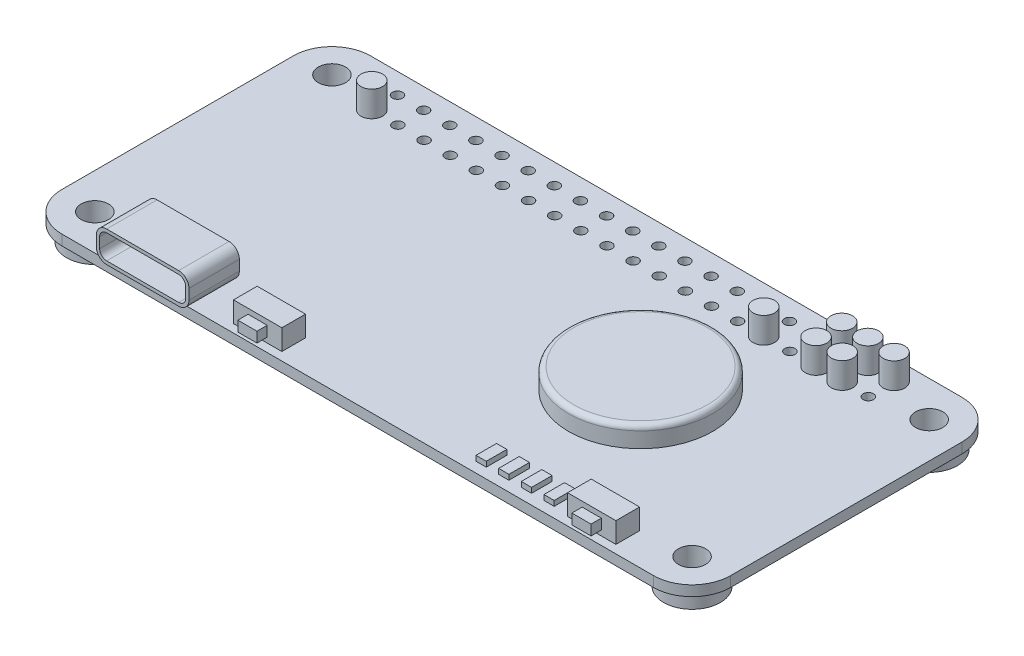
SolidWorks part; units mm, degrees
ref_plane "Front Plane" through (0, 0, 0) normal (0, 0, 1) x (1, 0, 0)
ref_plane "Top Plane" through (0, 0, 0) normal (0, 1, 0) x (1, 0, 0)
ref_plane "Right Plane" through (0, 0, 0) normal (1, 0, 0) x (0, 0, -1)
sketch "Sketch1" plane through (0, 0, 0) normal (0, 1, 0) x (1, 0, 0)
  line L1 (-28.75, 15) -> (28.75, 15)
  line L2 (-32.5, 11.25) -> (-32.5, -11.25)
  line L3 (-28.75, -15) -> (28.75, -15)
  line L4 (32.5, 11.25) -> (32.5, -11.25)
  line L5 (-32.5, 15) -> (32.5, -15) construction
  line L6 (-32.5, -15) -> (32.5, 15) construction
  arc A0 (-32.5, -11.25) -> (-28.75, -15) centre (-28.75, -11.25) ccw
  arc A1 (28.75, -15) -> (32.5, -11.25) centre (28.75, -11.25) ccw
  arc A2 (28.75, 15) -> (32.5, 11.25) centre (28.75, 11.25) cw
  arc A3 (-28.75, 15) -> (-32.5, 11.25) centre (-28.75, 11.25) ccw
  point P0 (0, 0)
  dimension "D3" = 3.75
  dimension "D1" = 65
  dimension "D2" = 30
extrude "Boss-Extrude1" add sketch "Sketch1" along normal blind 1 contours L1 A2 L4 A1 L3 A0 L2 A3
sketch "Sketch2" plane through (0, 1, 0) normal (0, 1, 0) x (1, 0, 0)
  line L0 (0, 15) -> (0, -15) construction
  line L1 (-28.75, 15) -> (28.75, 15) construction
  line L2 (-28.75, -15) -> (28.75, -15) construction
  line L3 (-32.5, 0) -> (32.5, 0) construction
  line L4 (-32.5, 11.25) -> (-32.5, -11.25) construction
  line L5 (32.5, 11.25) -> (32.5, -11.25) construction
  circle A0 centre (-29.025, 11.525) radius 1.325
  circle A2 centre (29.025, 11.525) radius 1.325
  circle A3 centre (29.025, -11.525) radius 1.325
  circle A4 centre (-29.025, -11.525) radius 1.325
  dimension "D1" = 2.65
  dimension "D2" = 2.15
  dimension "D3" = 2.15
extrude "Cut-Extrude1" cut sketch "Sketch2" against normal through all
sketch "Sketch3" plane through (0, 1, 0) normal (0, 1, 0) x (1, 0, 0)
  line L0 (-24.128, 13) -> (-24.128, 10.5) construction
  line L3 (-28.75, 15) -> (28.75, 15) construction
  line L5 (-32.5, 11.25) -> (-32.5, -11.25) construction
  circle A0 centre (-24.128, 13) radius 0.5
  circle A1 centre (-24.128, 10.5) radius 0.5
  dimension "D1" = 1
  dimension "D3" = 1.5
  dimension "D4" = 7.872
  dimension "D2" = 2.5
extrude "Cut-Extrude2" cut sketch "Sketch3" against normal through all
pattern_linear "LPattern1" count 20 spacing 2.54 along (1, 0, 0) of "Cut-Extrude2"
sketch "Sketch15" plane through (0, 0, 15) normal (0, 0, 1) x (1, 0, 0)
  line L0 (-28.75, 1) -> (28.75, 1) construction
  line L2 (-24, 4) -> (-17, 4)
  line L3 (-25, 3) -> (-25, 2)
  line L4 (-24, 1) -> (-17, 1)
  line L5 (-16, 3) -> (-16, 2)
  line L6 (-32.5, 1) -> (-32.5, 0) construction
  line L9 (15.325, 0) -> (15.325, 5.5788) construction
  line L10 (-28.75, 0) -> (28.75, 0) construction
  arc A0 (-17, 4) -> (-16, 3) centre (-17, 3) cw
  arc A1 (-17, 1) -> (-16, 2) centre (-17, 2) ccw
  arc A2 (-25, 2) -> (-24, 1) centre (-24, 2) ccw
  arc A3 (-24, 4) -> (-25, 3) centre (-24, 3) ccw
  point P10 (-16, 4)
  point P13 (-16, 1)
  point P18 (-25, 4)
  dimension "D4" = 1
  dimension "D1" = 9
  dimension "D2" = 3
  dimension "D3" = 7.5
extrude "Boss-Extrude6" add sketch "Sketch15" along normal blind 0.4 and the other way blind 4.5
sketch "Sketch16" plane through (0, 0, 15.4) normal (0, 0, 1) x (1, 0, 0)
  line L4 (-17, 3.68) -> (-24, 3.68)
  line L5 (-17, 3.68) -> (-24, 3.68)
  line L6 (-24.68, 3) -> (-24.68, 2)
  line L7 (-24.68, 3) -> (-24.68, 2)
  line L8 (-24, 1.32) -> (-17, 1.32)
  line L9 (-24, 1.32) -> (-17, 1.32)
  line L10 (-16.32, 2) -> (-16.32, 3)
  line L11 (-16.32, 2) -> (-16.32, 3)
  arc A4 (-16.32, 3) -> (-17, 3.68) centre (-17, 3) ccw
  arc A5 (-16.32, 3) -> (-17, 3.68) centre (-17, 3) ccw
  arc A6 (-24, 3.68) -> (-24.68, 3) centre (-24, 3) ccw
  arc A7 (-24, 3.68) -> (-24.68, 3) centre (-24, 3) ccw
  arc A8 (-24.68, 2) -> (-24, 1.32) centre (-24, 2) ccw
  arc A9 (-24.68, 2) -> (-24, 1.32) centre (-24, 2) ccw
  arc A10 (-17, 1.32) -> (-16.32, 2) centre (-17, 2) ccw
  arc A11 (-17, 1.32) -> (-16.32, 2) centre (-17, 2) ccw
  dimension "D2" = 0.32
extrude "Cut-Extrude9" cut sketch "Sketch16" against normal blind 5.25
sketch "草图1" plane through (0, 1, 0) normal (0, 1, 0) x (1, 0, 0)
  line L1 (-12.87, -11.9) -> (-8.17, -11.9)
  line L2 (-12.87, -11.9) -> (-12.87, -14.2)
  line L3 (-12.87, -14.2) -> (-8.17, -14.2)
  line L4 (-8.17, -11.9) -> (-8.17, -14.2)
  line L5 (-28.75, -15) -> (-24, -15) construction
  line L6 (-16, -10.5) -> (-16, -15.4) construction
  line L7 (32.5, 11.25) -> (32.5, -11.25) construction
  line L8 (24.3, -11.9) -> (19.6, -11.9)
  line L9 (24.3, -11.9) -> (24.3, -14.2)
  line L10 (24.3, -14.2) -> (19.6, -14.2)
  line L11 (19.6, -11.9) -> (19.6, -14.2)
  dimension "D1" = 4.7
  dimension "D2" = 2.3
  dimension "D3" = 3.13
  dimension "D4" = 0.8
  dimension "D5" = 8.2
extrude "凸台-拉伸1" add sketch "草图1" along normal blind 2
sketch "草图2" plane through (0, 0, 14.2) normal (0, 0, 1) x (1, 0, 0)
  line L0 (-12.87, 3) -> (-8.17, 3) construction
  line L5 (-11.45, 2.5) -> (-9.59, 2.5)
  line L6 (-11.45, 2.5) -> (-11.45, 1.5)
  line L7 (-11.45, 1.5) -> (-9.59, 1.5)
  line L8 (-9.59, 2.5) -> (-9.59, 1.5)
  line L9 (-11.45, 2.5) -> (-9.59, 1.5) construction
  line L10 (-11.45, 1.5) -> (-9.59, 2.5) construction
  line L11 (-8.17, 3) -> (-8.17, 1) construction
  line L12 (19.6, 3) -> (24.3, 3) construction
  line L13 (21.02, 2.5) -> (22.88, 2.5)
  line L14 (21.02, 2.5) -> (21.02, 1.5)
  line L15 (21.02, 1.5) -> (22.88, 1.5)
  line L16 (22.88, 2.5) -> (22.88, 1.5)
  line L17 (21.02, 2.5) -> (22.88, 1.5) construction
  line L18 (21.02, 1.5) -> (22.88, 2.5) construction
  line L19 (24.3, 3) -> (24.3, 1) construction
  point P0 (-10.52, 2)
  point P5 (21.95, 2)
  point P8 (-10.52, 3)
  point P12 (-8.17, 2)
  point P19 (21.95, 3)
  point P23 (24.3, 2)
  dimension "D1" = 1.86
  dimension "D2" = 1
extrude "凸台-拉伸2" add sketch "草图2" along normal blind 1
sketch "草图9" plane through (0, 0, 0) normal (0, -1, 0) x (1, 0, 0)
  circle A0 centre (29.025, 11.525) radius 2.75
  circle A1 centre (29.025, -11.525) radius 2.75
  circle A2 centre (-29.025, 11.525) radius 2.75
  circle A3 centre (-29.025, -11.525) radius 2.75
  circle A4 centre (29.025, 11.525) radius 1.325 construction
  circle A5 centre (29.025, -11.525) radius 1.325 construction
  circle A6 centre (-29.025, 11.525) radius 1.325 construction
  circle A7 centre (-29.025, -11.525) radius 1.325 construction
  circle A8 centre (29.025, 11.525) radius 1.325
  circle A9 centre (29.025, -11.525) radius 1.325
  circle A10 centre (-29.025, 11.525) radius 1.325
  circle A11 centre (-29.025, -11.525) radius 1.325
  dimension "D1" = 5.5
extrude "凸台-拉伸8" add sketch "草图9" along normal blind 1.5
sketch "草图10" plane through (0, 1, 0) normal (0, 1, 0) x (1, 0, 0)
  circle A0 centre (24.132, 13) radius 1.05
  circle A1 centre (21.592, 13) radius 1.05
  circle A2 centre (19.052, 13) radius 1.05
  circle A3 centre (21.592, 10.5) radius 1.05
  circle A4 centre (19.052, 10.5) radius 1.05
  circle A5 centre (-24.128, 10.5) radius 1.05
  circle A6 centre (13.972, 10.5) radius 1.05
  dimension "D1" = 2.1
extrude "凸台-拉伸9" add sketch "草图10" along normal blind 2.5
sketch "草图11" plane through (0, 1, 0) normal (0, -1, 0) x (1, 0, 0)
  circle A0 centre (24.132, -13) radius 0.5
  circle A1 centre (21.592, -13) radius 0.5
  circle A2 centre (21.592, -10.5) radius 0.5
  circle A3 centre (19.052, -10.5) radius 0.5
  circle A5 centre (19.052, -13) radius 0.5
  circle A7 centre (-24.128, -10.5) radius 0.5
extrude "凸台-拉伸10" add sketch "草图11" along normal blind 3
sketch "草图12" plane through (0, 1, 0) normal (0, 1, 0) x (1, 0, 0)
  line L1 (32.5, 11.25) -> (32.5, -11.25) construction
  line L2 (-28.75, 15) -> (28.75, 15) construction
  circle A0 centre (12.5, 0) radius 7
  dimension "D1" = 14
  dimension "D2" = 20
  dimension "D3" = 15
extrude "凸台-拉伸11" add sketch "草图12" along normal blind 2
sketch "草图13" plane through (0, 1, 0) normal (0, 1, 0) x (1, 0, 0)
  line L0 (19.6, -11.9) -> (19.6, -14.2) construction
  line L1 (17.1, -12) -> (18.1, -12)
  line L2 (17.1, -12) -> (17.1, -14)
  line L3 (17.1, -14) -> (18.1, -14)
  line L4 (18.1, -12) -> (18.1, -14)
  line L5 (17.1, -12) -> (18.1, -14) construction
  line L6 (17.1, -14) -> (18.1, -12) construction
  line L7 (14.9, -12) -> (15.9, -12)
  line L8 (14.9, -12) -> (14.9, -14)
  line L9 (14.9, -14) -> (15.9, -14)
  line L10 (15.9, -12) -> (15.9, -14)
  line L11 (14.9, -12) -> (15.9, -14) construction
  line L12 (14.9, -14) -> (15.9, -12) construction
  line L13 (12.7, -12) -> (13.7, -12)
  line L14 (12.7, -12) -> (12.7, -14)
  line L15 (12.7, -14) -> (13.7, -14)
  line L16 (13.7, -12) -> (13.7, -14)
  line L17 (12.7, -12) -> (13.7, -14) construction
  line L18 (12.7, -14) -> (13.7, -12) construction
  line L19 (10.5, -12) -> (11.5, -12)
  line L20 (10.5, -12) -> (10.5, -14)
  line L21 (10.5, -14) -> (11.5, -14)
  line L22 (11.5, -12) -> (11.5, -14)
  line L23 (10.5, -12) -> (11.5, -14) construction
  line L24 (10.5, -14) -> (11.5, -12) construction
  line L25 (-17, -15) -> (28.75, -15) construction
  point P0 (17.6, -13)
  point P5 (15.4, -13)
  point P10 (13.2, -13)
  point P15 (11, -13)
  dimension "D1" = 1
  dimension "D2" = 2
  dimension "D3" = 1.2
  dimension "D4" = 1.2
  dimension "D5" = 1.2
  dimension "D6" = 1.5
  dimension "D7" = 1
extrude "凸台-拉伸12" add sketch "草图13" along normal blind 0.5
fillet "圆角1" radius 0.5 1 edges at (12.5, 3, 7)
sketch "草图14" plane through (0, 0, 10.5) normal (0, 0, -1) x (-1, 0, 0)
  line L4 (16, 3) -> (16, 2)
  line L5 (17, 1) -> (24, 1)
  line L6 (25, 2) -> (25, 3)
  line L7 (24, 4) -> (17, 4)
  line L8 (16, 3) -> (16, 2)
  line L9 (17, 1) -> (24, 1)
  line L10 (25, 2) -> (25, 3)
  line L11 (24, 4) -> (17, 4)
  arc A4 (17, 4) -> (16, 3) centre (17, 3) ccw
  arc A5 (16, 2) -> (17, 1) centre (17, 2) ccw
  arc A6 (24, 1) -> (25, 2) centre (24, 2) ccw
  arc A7 (25, 3) -> (24, 4) centre (24, 3) ccw
  arc A8 (17, 4) -> (16, 3) centre (17, 3) ccw
  arc A9 (16, 2) -> (17, 1) centre (17, 2) ccw
  arc A10 (24, 1) -> (25, 2) centre (24, 2) ccw
  arc A11 (25, 3) -> (24, 4) centre (24, 3) ccw
  dimension "D1" = 0
extrude "凸台-拉伸13" add sketch "草图14" against normal blind 1
